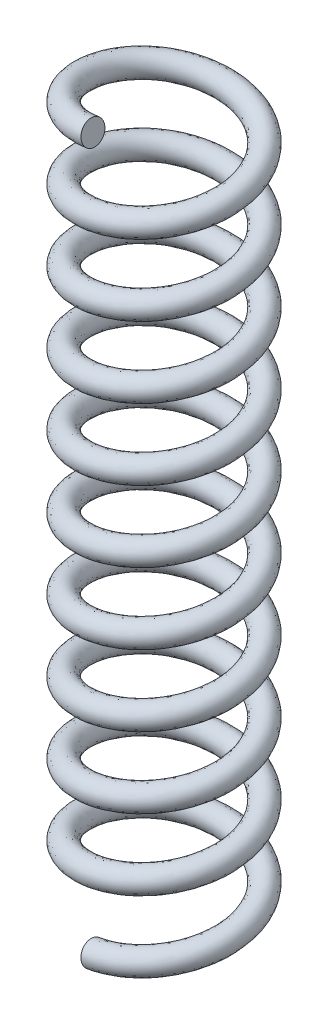
SolidWorks part; units mm, degrees
ref_plane "Front" through (0, 0, 0) normal (0, 0, 1) x (1, 0, 0)
ref_plane "Top" through (0, 0, 0) normal (0, 1, 0) x (1, 0, 0)
ref_plane "Right" through (0, 0, 0) normal (1, 0, 0) x (0, 0, -1)
sketch "Sketch1" plane through (0, 0, 0) normal (0, 1, 0) x (1, 0, 0)
  circle A0 centre (0, 0) radius 15
  dimension "D1" = 30
curve "Helix/Spiral2" pitch 15 height 150 turns 10
ref_plane "Plane2" through (0, 0, 15) normal (0.9876, 0.1572, 0) x (0, 0, -1)
sketch "Sketch4" plane through (0, 0, 15) normal (0.9876, 0.1572, 0) x (0, 0, -1)
  circle A0 centre (0, 0) radius 2.5
  dimension "D1" = 5
sweep "Sweep2" add profiles "Sketch4" path "Helix/Spiral2"
